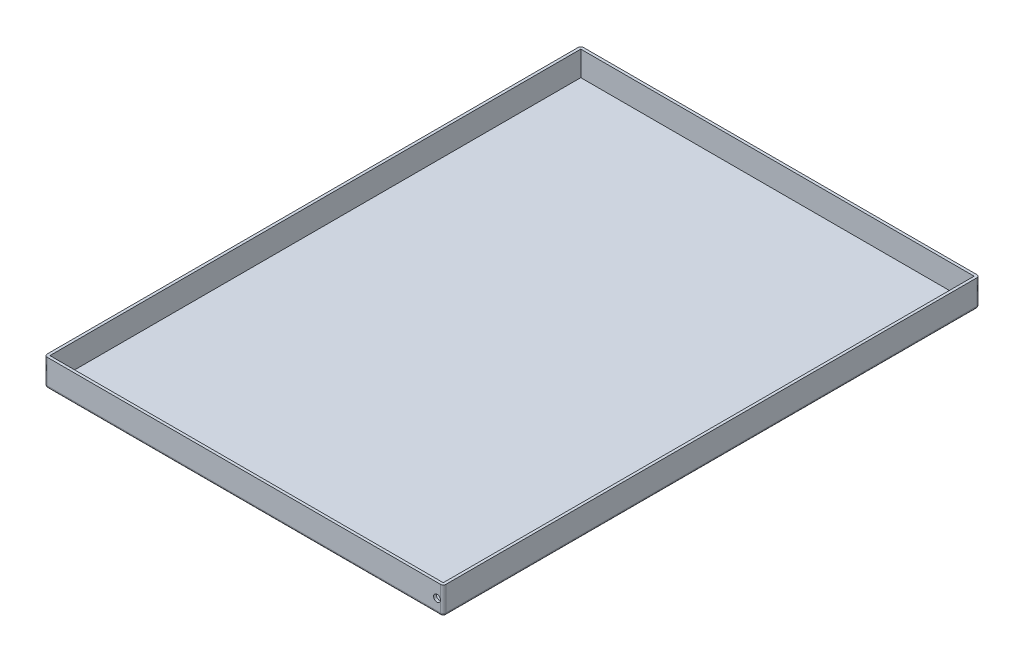
SolidWorks part; units mm, degrees
ref_plane "Front Plane" through (0, 0, 0) normal (0, 0, 1) x (1, 0, 0)
ref_plane "Top Plane" through (0, 0, 0) normal (0, 1, 0) x (1, 0, 0)
ref_plane "Right Plane" through (0, 0, 0) normal (1, 0, 0) x (0, 0, -1)
sketch "Sketch1" plane through (0, 0, 0) normal (0, 1, 0) x (1, 0, 0)
  line L1 (0, 0) -> (290, 0)
  line L2 (0, 0) -> (0, 390)
  line L3 (0, 390) -> (290, 390)
  line L4 (290, 0) -> (290, 390)
  dimension "D1" = 290
  dimension "D2" = 390
extrude "Boss-Extrude1" add sketch "Sketch1" along normal blind 20
sketch "Sketch2" plane through (0, 20, 0) normal (0, 1, 0) x (1, 0, 0)
  line L0 (290, 390) -> (0, 390) construction
  line L1 (2, 388) -> (288, 388)
  line L2 (2, 388) -> (2, 2)
  line L3 (2, 2) -> (288, 2)
  line L4 (288, 388) -> (288, 2)
  line L5 (290, 0) -> (290, 390) construction
  line L6 (0, 0) -> (290, 0) construction
  line L7 (0, 390) -> (0, 0) construction
  dimension "D1" = 2
  dimension "D2" = 2
  dimension "D3" = 2
  dimension "D4" = 2
extrude "Cut-Extrude1" cut sketch "Sketch2" against normal blind 18
fillet "Fillet1" radius 2 8 edges at (145, 0, 0) (290, 0, -195) (145, 0, -390) (0, 0, -195) (0, 10, 0) (290, 10, 0) (290, 10, -390) (0, 10, -390)
sketch "Sketch3" plane through (0, 0, -390) normal (0, 0, -1) x (-1, 0, 0)
  line L0 (-288, 20) -> (-2, 20) construction
  line L1 (-288, 20) -> (-288, 2) construction
  circle A0 centre (-285.5, 10) radius 2.5
  dimension "D1" = 5
  dimension "D2" = 10
extrude "Cut-Extrude2" cut sketch "Sketch3" against normal through all
sketch "Sketch4" plane through (0, 0, 0) normal (0, -1, 0) x (-1, 0, 0)
  line L0 (-2, 2) -> (-2, 388) construction
  line L1 (-32, 75) -> (-62, 75)
  line L2 (-32, 75) -> (-32, 115)
  line L3 (-32, 115) -> (-62, 115)
  line L4 (-62, 75) -> (-62, 115)
  line L5 (-32, 275) -> (-62, 275)
  line L6 (-32, 275) -> (-32, 315)
  line L7 (-32, 315) -> (-62, 315)
  line L8 (-62, 275) -> (-62, 315)
  line L9 (-288, 390) -> (-2, 390) construction
  line L10 (-2, 0) -> (-288, 0) construction
  dimension "D1" = 30
  dimension "D2" = 40
  dimension "D3" = 30
  dimension "D4" = 75
  dimension "D5" = 75
extrude "Boss-Extrude2" add sketch "Sketch4" along normal blind 5 separate body
fillet "Fillet2" radius 2 8 edges at (47, -5, -75) (62, -5, -95) (47, -5, -115) (32, -5, -95) (62, -2.5, -75) (62, -2.5, -115) (32, -2.5, -115) (32, -2.5, -75)
fillet "Fillet3" radius 2 8 edges at (47, -5, -275) (62, -5, -295) (47, -5, -315) (32, -5, -295) (62, -2.5, -275) (62, -2.5, -315) (32, -2.5, -315) (32, -2.5, -275)
